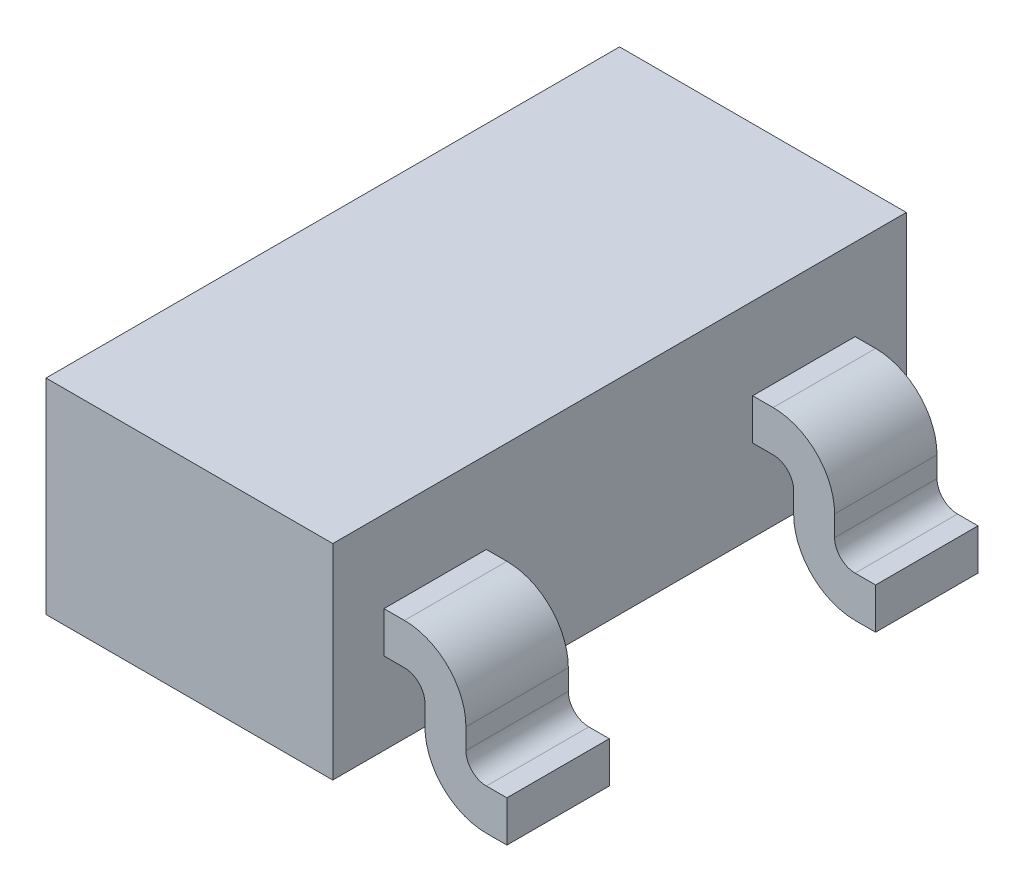
SolidWorks part; units mm, degrees
ref_plane "Front Plane" through (0, 0, 0) normal (0, 0, 1) x (1, 0, 0)
ref_plane "Top Plane" through (0, 0, 0) normal (0, 1, 0) x (1, 0, 0)
ref_plane "Right Plane" through (0, 0, 0) normal (1, 0, 0) x (0, 0, -1)
sketch "BaseS" plane through (0, 0, 0) normal (0, 1, 0) x (1, 0, 0)
  line L1 (-0.7, 1.4) -> (0.7, 1.4)
  line L2 (-0.7, 1.4) -> (-0.7, -1.4)
  line L3 (-0.7, -1.4) -> (0.7, -1.4)
  line L4 (0.7, 1.4) -> (0.7, -1.4)
  line L5 (-0.7, 1.4) -> (0.7, -1.4) construction
  line L6 (-0.7, -1.4) -> (0.7, 1.4) construction
  point P0 (0, 0)
  dimension "Length" = 2.8
  dimension "Width" = 1.4
extrude "Base" add sketch "BaseS" along normal mid plane 1
sketch "Leg1S" plane through (0, 0, 0) normal (0, 0, 1) x (1, 0, 0)
  line L0 (-0.7, 0) -> (-0.8, 0)
  line L1 (-1, -0.2) -> (-1, -0.3)
  line L2 (-1.2, -0.5) -> (-1.3, -0.5)
  line L3 (-0.7, 0.5) -> (-0.7, -0.5) construction
  line L4 (-0.7, -0.5) -> (0.7, -0.5) construction
  line L5 (-0.7, 0.5) -> (-0.7, -0.5) construction
  arc A0 (-1.2, -0.5) -> (-1, -0.3) centre (-1.2, -0.3) ccw
  arc A1 (-1, -0.2) -> (-0.8, 0) centre (-0.8, -0.2) cw
  dimension "D1" = 0.2
  dimension "D2" = 0.6
extrude "Leg1" add sketch "Leg1S" along normal mid plane 0.5 thin thin type mid plane wall 0.2
ref_plane "LegRP" through (0, 0, 0.9) normal (0, 0, 1) x (1, 0, 0)
sketch "Leg2S" plane through (0, 0, 0.9) normal (0, 0, 1) x (1, 0, 0)
  line L0 (-1.2, -0.5) -> (-1.3, -0.5) construction
  line L1 (-1, -0.2) -> (-1, -0.3) construction
  line L2 (-0.7, 0) -> (-0.8, 0) construction
  line L3 (-1.2, -0.5) -> (-1.3, -0.5) construction
  line L4 (-1, -0.2) -> (-1, -0.3) construction
  line L5 (-0.7, 0) -> (-0.8, 0) construction
  line L6 (0, -0.605) -> (0, 0.605) construction
  line L7 (0.7, 0) -> (0.8, 0)
  line L8 (1, -0.2) -> (1, -0.3)
  line L9 (1.2, -0.5) -> (1.3, -0.5)
  arc A0 (-1.2, -0.5) -> (-1, -0.3) centre (-1.2, -0.3) ccw construction
  arc A1 (-0.8, 0) -> (-1, -0.2) centre (-0.8, -0.2) ccw construction
  arc A2 (-1.2, -0.5) -> (-1, -0.3) centre (-1.2, -0.3) ccw construction
  arc A3 (-0.8, 0) -> (-1, -0.2) centre (-0.8, -0.2) ccw construction
  arc A4 (0.8, 0) -> (1, -0.2) centre (0.8, -0.2) cw
  arc A5 (1.2, -0.5) -> (1, -0.3) centre (1.2, -0.3) cw
extrude "Leg2" add sketch "Leg2S" along normal mid plane 0.5 thin thin type mid plane wall 0.2
mirror "Leg2M" about plane through (0, 0, 0) normal (0, 0, 1) of "Leg2"
ref_point "Point1"
equation "\"Width@Leg2\"=\"Width@Leg1\""
